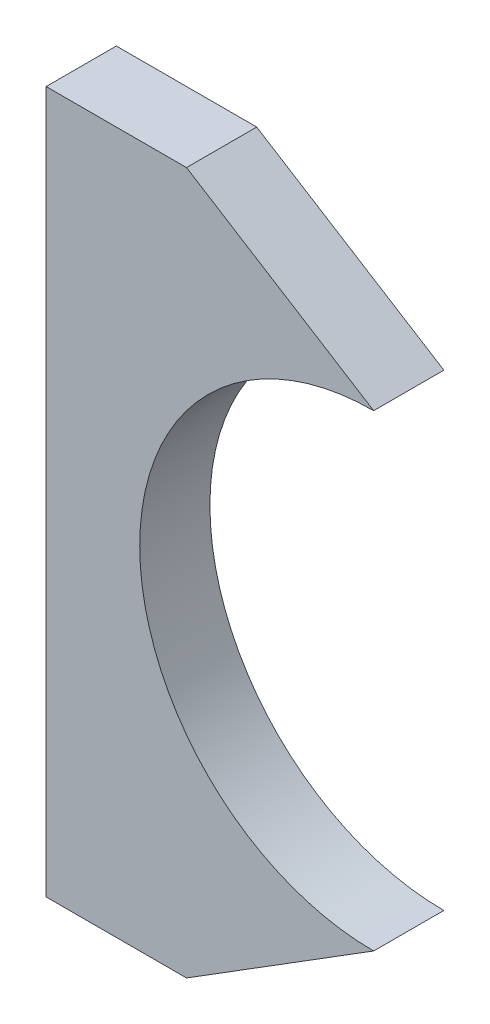
SolidWorks part; units mm, degrees
material "Tungsten"
ref_plane "Front Plane" through (0, 0, 0) normal (0, 0, 1) x (1, 0, 0)
ref_plane "Top Plane" through (0, 0, 0) normal (0, 1, 0) x (1, 0, 0)
ref_plane "Right Plane" through (0, 0, 0) normal (1, 0, 0) x (0, 0, -1)
sketch "Sketch1" plane through (0, 0, 0) normal (0, 0, 1) x (1, 0, 0)
  line L0 (-70, 75) -> (-40, 75)
  line L1 (-70, 75) -> (-70, -75)
  line L2 (-70, -75) -> (-40, -75)
  line L3 (-40, -75) -> (0, -50)
  line L4 (-40, 75) -> (0, 50)
  arc A0 (0, 50) -> (0, -50) centre (0, 0) ccw
  dimension "D1" = 100
  dimension "D2" = 75
  dimension "D3" = 75
  dimension "D4" = 70
  dimension "D5" = 30
  dimension "D6" = 30
extrude "Boss-Extrude1" add sketch "Sketch1" along normal mid plane 15
